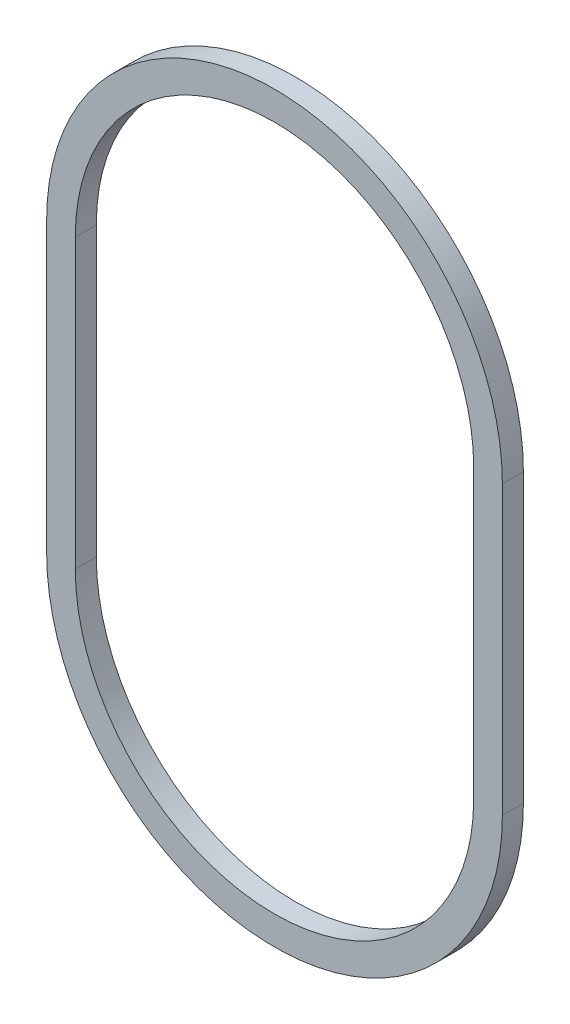
SolidWorks part; units mm, degrees
ref_plane "Front Plane" through (0, 0, 0) normal (0, 0, 1) x (1, 0, 0)
ref_plane "Top Plane" through (0, 0, 0) normal (0, 1, 0) x (1, 0, 0)
ref_plane "Right Plane" through (0, 0, 0) normal (1, 0, 0) x (0, 0, -1)
sketch "Sketch1" plane through (0, 0, 0) normal (0, 0, 1) x (1, 0, 0)
  line L0 (0, 0) -> (0, 8.81) construction
  line L1 (23.85, 0) -> (73.5278, 0) construction
  line L2 (-23.85, 15.04) -> (-23.85, -15.04)
  line L3 (23.85, 15.04) -> (23.85, -15.04)
  line L4 (0, 38.89) -> (0, 64.6364) construction
  line L5 (-20.85, 15.04) -> (-20.85, -15.04)
  line L6 (20.85, 15.04) -> (20.85, -15.04)
  arc A0 (23.85, 15.04) -> (-23.85, 15.04) centre (0, 15.04) ccw
  arc A1 (23.85, -15.04) -> (-23.85, -15.04) centre (0, -15.04) cw
  arc A2 (20.85, 15.04) -> (-20.85, 15.04) centre (0, 15.04) ccw
  arc A3 (20.85, -15.04) -> (-20.85, -15.04) centre (0, -15.04) cw
  dimension "D1" = 47.7
  dimension "D2" = 15.04
  dimension "D3" = 3
extrude "Boss-Extrude1" add sketch "Sketch1" along normal blind 2.2
